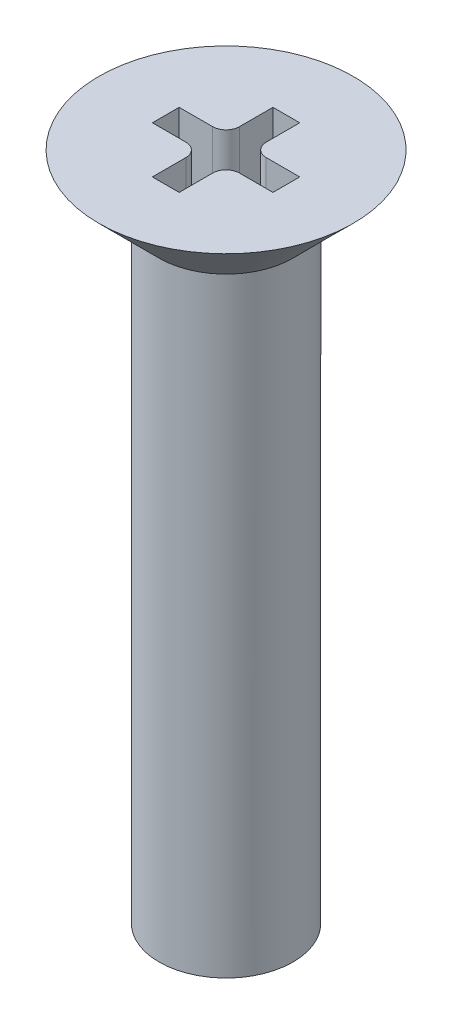
SolidWorks part; units mm, degrees
material "1023 Carbon Steel Sheet (SS)"
ref_plane "Front Plane" through (0, 0, 0) normal (0, 0, 1) x (1, 0, 0)
ref_plane "Top Plane" through (0, 0, 0) normal (0, 1, 0) x (1, 0, 0)
ref_plane "Right Plane" through (0, 0, 0) normal (1, 0, 0) x (0, 0, -1)
sketch "Sketch1" plane through (0, 0, 0) normal (1, 0, 0) x (0, 0, -1)
  line L0 (-1.9, 0) -> (1.9, 0) construction
  line L1 (-1.9, 0) -> (-1, -0.9) construction
  line L2 (-1, -0.9) -> (1, -0.9) construction
  line L3 (1, -0.9) -> (1.9, 0) construction
  line L4 (-1, -0.9) -> (-1, -1.2) construction
  line L5 (1, -0.9) -> (1, -1.2) construction
  line L6 (1, -1.2) -> (-1, -1.2) construction
  line L7 (0, 0.8723) -> (0, -0.1883) construction
  line L8 (0, 0) -> (-1.9, 0)
  line L9 (-1.9, 0) -> (-1, -0.9)
  line L10 (-1, -0.9) -> (-1, -1.2)
  line L11 (-1, -1.2) -> (0, -1.2)
  line L12 (0, 0) -> (0, -1.2)
  point P3 (0, -0.9)
  dimension "D1" = 3.8
  dimension "D2" = 90
  dimension "D3" = 2
  dimension "D4" = 1.2
revolve "Revolve1" add sketch "Sketch1" angle 360 about L7
sketch "Sketch2" plane through (0, -1.2, 0) normal (0, -1, 0) x (1, 0, 0)
  circle A0 centre (0, 0) radius 1
  dimension "D1" = 2
extrude "Boss-Extrude1" add sketch "Sketch2" along normal blind 8.8
sketch "Sketch3" plane through (0, 0, 0) normal (0, 1, 0) x (1, 0, 0)
  line L1 (-0.9, -0.2) -> (-0.4, -0.2)
  line L2 (-0.9, -0.2) -> (-0.9, 0.2)
  line L3 (-0.9, 0.2) -> (-0.4, 0.2)
  line L4 (0.9, -0.2) -> (0.9, 0.2)
  line L5 (-0.9, -0.2) -> (0.9, 0.2) construction
  line L6 (-0.9, 0.2) -> (0.9, -0.2) construction
  line L7 (-0.2, -0.9) -> (0.2, -0.9)
  line L8 (-0.2, -0.9) -> (-0.2, -0.4)
  line L9 (-0.2, 0.9) -> (0.2, 0.9)
  line L10 (0.2, -0.9) -> (0.2, -0.4)
  line L11 (-0.2, -0.9) -> (0.2, 0.9) construction
  line L12 (-0.2, 0.9) -> (0.2, -0.9) construction
  line L13 (-0.2, 0.4) -> (-0.2, 0.9)
  line L14 (0.4, 0.2) -> (0.9, 0.2)
  line L15 (0.2, 0.4) -> (0.2, 0.9)
  line L17 (0.4, -0.2) -> (0.9, -0.2)
  arc A0 (-0.4, 0.2) -> (-0.2, 0.4) centre (-0.4, 0.4) ccw
  arc A1 (0.2, 0.4) -> (0.4, 0.2) centre (0.4, 0.4) ccw
  arc A2 (0.4, -0.2) -> (0.2, -0.4) centre (0.4, -0.4) ccw
  arc A3 (-0.2, -0.4) -> (-0.4, -0.2) centre (-0.4, -0.4) ccw
  point P0 (0, 0)
  point P6 (0, 0)
  point P14 (-0.2, 0.2)
  point P19 (0.2, 0.2)
  point P23 (0.2, -0.2)
  dimension "D5" = 0.2
  dimension "D1" = 0.4
  dimension "D2" = 1.8
  dimension "D3" = 0.4
  dimension "D4" = 1.8
extrude "Cut-Extrude1" cut sketch "Sketch3" against normal blind 1
